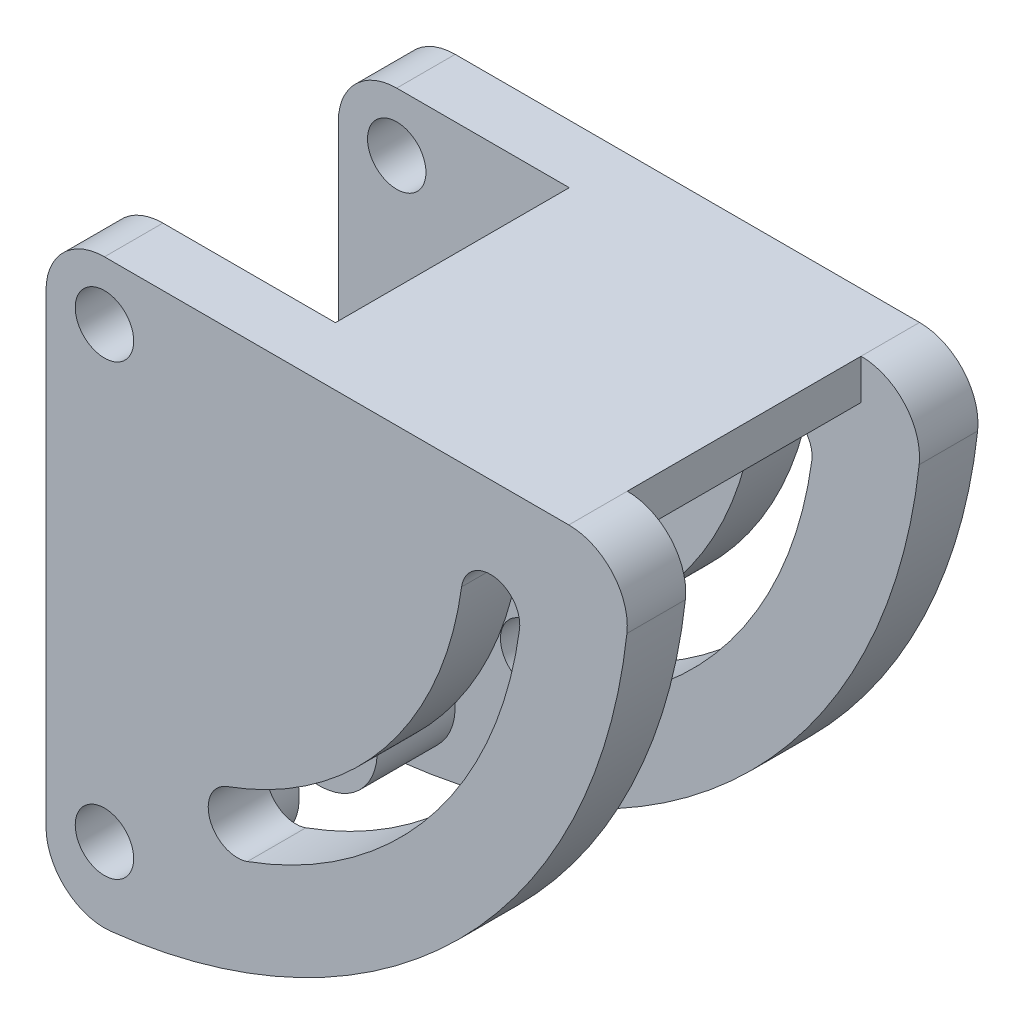
SolidWorks part; units mm, degrees
ref_plane "Front Plane" through (0, 0, 0) normal (0, 0, 1) x (1, 0, 0)
ref_plane "Top Plane" through (0, 0, 0) normal (0, 1, 0) x (1, 0, 0)
ref_plane "Right Plane" through (0, 0, 0) normal (1, 0, 0) x (0, 0, -1)
sketch "Sketch1" plane through (0, 0, 0) normal (0, 0, 1) x (1, 0, 0)
  line L0 (0, 0) -> (30, 0)
  line L1 (0, 0) -> (0, -30)
  arc A0 (0, -30) -> (30, 0) centre (0, 0) ccw
  circle A1 centre (3, -26) radius 1.5
  arc A4 (22.8157, -5.7086) -> (9.825, -21.7995) centre (3, -3) cw construction
  circle A7 centre (3, -3) radius 1.5
  arc A8 (21.3296, -5.5055) -> (9.3131, -20.3895) centre (3, -3) cw
  arc A9 (10.3369, -23.2094) -> (24.3019, -5.9118) centre (3, -3) ccw
  arc A10 (24.3019, -5.9118) -> (21.3296, -5.5055) centre (22.8157, -5.7086) ccw
  arc A11 (9.3131, -20.3895) -> (10.3369, -23.2094) centre (9.825, -21.7995) ccw
  dimension "D2" = 3
  dimension "D3" = 3
  dimension "D8" = 30
  dimension "D1" = 20
  dimension "D4" = 3
  dimension "D5" = 3
  dimension "D6" = 4
  dimension "D7" = 3
extrude "Boss-Extrude1" add sketch "Sketch1" along normal blind 3
pattern_linear "LPattern1" count 2 spacing 15 along (0, 0, 1) of "Boss-Extrude1"
fillet "Fillet2" radius 3 3 edges at (0, -30, 1.5) (0, 0, 1.5) (30, 0, 1.5)
fillet "Fillet3" radius 3 3 edges at (0, -30, 16.5) (0, 0, 16.5) (30, 0, 16.5)
sketch "Sketch2" plane through (0, 0, 3) normal (0, 0, 1) x (1, 0, 0)
  line L0 (26.8328, 0) -> (3, 0) construction
  line L1 (11.8553, 0) -> (26.8328, 0)
  line L2 (11.8553, 0) -> (11.8553, -2.0588)
  line L3 (11.8553, -2.0588) -> (26.8328, -2.0588)
  line L4 (26.8328, 0) -> (26.8328, -2.0588)
extrude "Boss-Extrude2" add sketch "Sketch2" along normal up to next (15 mm away)
sketch "Sketch3" plane through (0, 0, 15) normal (0, 0, -1) x (-1, 0, 0)
  circle A0 centre (-3, -26) radius 3
  circle A2 centre (-3, -26) radius 1.5
  circle A3 centre (-3, -26) radius 1.5 construction
  dimension "D1" = 6
extrude "Boss-Extrude3" add sketch "Sketch3" along normal blind 4
pattern_linear "LPattern2" count 2 spacing 8 along (0, 0, -1) of "Boss-Extrude3"
